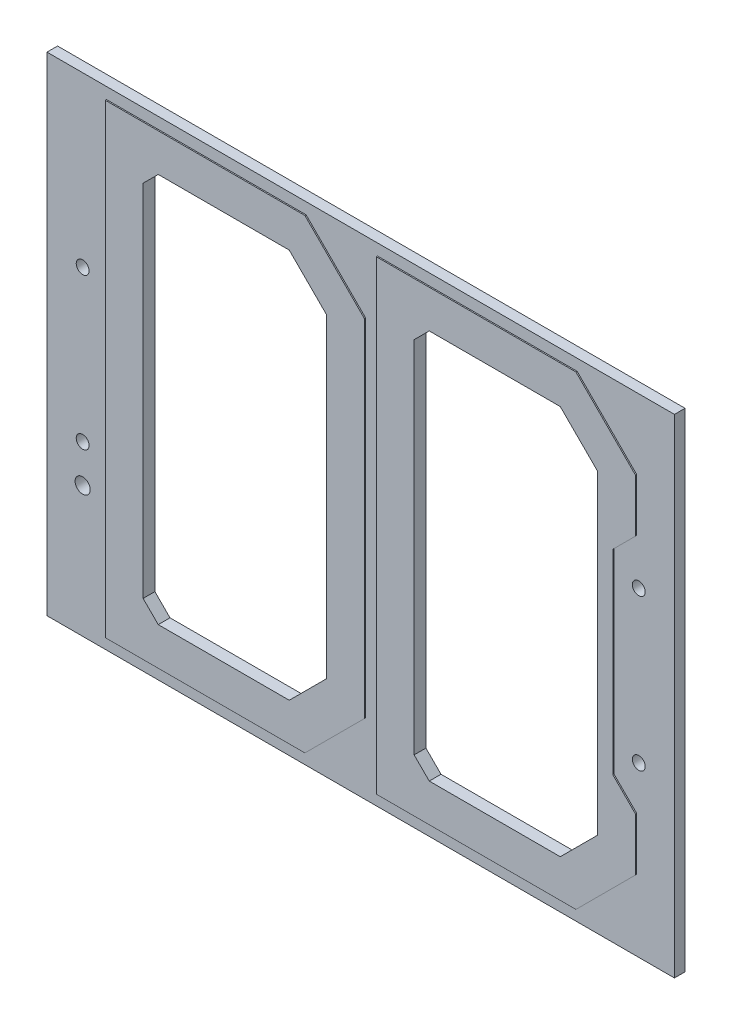
SolidWorks part; units mm, degrees
ref_plane "Front Plane" through (0, 0, 0) normal (0, 0, 1) x (1, 0, 0)
ref_plane "Top Plane" through (0, 0, 0) normal (0, 1, 0) x (1, 0, 0)
ref_plane "Right Plane" through (0, 0, 0) normal (1, 0, 0) x (0, 0, -1)
sketch "Sketch1" plane through (0, 0, 0) normal (0, 0, 1) x (1, 0, 0)
  line L0 (-46.7106, 41) -> (-46.7106, -41) construction
  line L1 (-52.705, -41) -> (52.705, -41)
  line L2 (-52.705, -41) -> (-52.705, 41)
  line L3 (-52.705, 41) -> (52.705, 41)
  line L4 (52.705, -41) -> (52.705, 41)
  line L5 (-52.705, -41) -> (52.705, 41) construction
  line L6 (-52.705, 41) -> (52.705, -41) construction
  line L7 (46.7106, 41) -> (46.7106, -41) construction
  circle A3 centre (46.7106, 12.7) radius 1.0795
  circle A4 centre (46.7106, -12.7) radius 1.0795
  circle A5 centre (-46.7106, 12.7) radius 1.0795
  circle A6 centre (-46.7106, -12.7) radius 1.0795
  circle A10 centre (-46.7106, -19.05) radius 1.27
  point P0 (0, 0)
  dimension "D15" = 2.54
  dimension "D3" = 2.159
  dimension "D1" = 82
  dimension "D2" = 105.41
  dimension "D7" = 5.9944
  dimension "D11" = 5.9944
  dimension "D4" = 28.3
  dimension "D5" = 6.35
  dimension "D9" = 28.3
extrude "Boss-Extrude1" add sketch "Sketch1" along normal blind 1.778
sketch "Sketch2" plane through (0, 0, 1.778) normal (0, 0, 1) x (1, 0, 0)
  line L0 (-9.175, 39.095) -> (0.825, 29.095)
  line L1 (-42.705, 39.095) -> (-9.175, 39.095)
  line L2 (-42.705, 39.095) -> (-42.705, -39.095)
  line L3 (-42.705, -39.095) -> (-9.175, -39.095)
  line L4 (0.825, 29.095) -> (0.825, -29.095)
  line L5 (-42.705, 39.095) -> (0.825, -39.095) construction
  line L6 (-42.705, -39.095) -> (0.825, 39.095) construction
  line L11 (46.355, 20.205) -> (42.545, 16.395)
  line L12 (42.545, 16.395) -> (42.545, -16.395)
  line L17 (42.545, -16.395) -> (46.355, -20.205)
  line L18 (-52.705, 41) -> (52.705, 41) construction
  line L23 (-52.705, -41) -> (52.705, -41) construction
  line L24 (46.355, -20.205) -> (46.355, -29.095)
  line L43 (2.825, 39.095) -> (36.355, 39.095)
  line L44 (2.825, 39.095) -> (2.825, -39.095)
  line L45 (2.825, -39.095) -> (36.355, -39.095)
  line L46 (46.355, 29.095) -> (46.355, 20.205)
  line L47 (2.825, 39.095) -> (46.355, -39.095) construction
  line L48 (2.825, -39.095) -> (46.355, 39.095) construction
  line L49 (0.825, -29.095) -> (-9.175, -39.095)
  line L62 (36.355, -39.095) -> (46.355, -29.095)
  line L63 (36.355, 39.095) -> (46.355, 29.095)
  line L64 (-52.705, -41) -> (-52.705, 41) construction
  line L65 (52.705, -41) -> (52.705, 41) construction
  point P4 (-20.94, 0)
  point P39 (24.59, 0)
  point P76 (52.705, 0)
  dimension "D25" = 10
  dimension "D26" = 6.35
  dimension "D3" = 2
  dimension "D6" = 3.81
  dimension "D7" = 45
  dimension "D8" = 45
  dimension "D9" = 8.89
  dimension "D10" = 8.89
  dimension "D11" = 1.905
  dimension "D12" = 1.905
extrude "Boss-Extrude2" add sketch "Sketch2" along normal blind 0.2
sketch "Sketch3" plane through (0, 0, 1.978) normal (0, 0, 1) x (1, 0, 0)
  line L0 (-36.355, -32.745) -> (-36.355, 32.745)
  line L1 (-36.355, 32.745) -> (-11.8053, 32.745)
  line L2 (-11.8053, 32.745) -> (-5.525, 26.4647)
  line L3 (-5.525, 26.4647) -> (-5.525, -26.4647)
  line L4 (-5.525, -26.4647) -> (-11.8053, -32.745)
  line L5 (-11.8053, -32.745) -> (-36.355, -32.745)
  line L6 (9.175, -32.745) -> (9.175, 32.745)
  line L7 (9.175, 32.745) -> (33.7247, 32.745)
  line L8 (33.7247, 32.745) -> (40.005, 26.4647)
  line L9 (40.005, 26.4647) -> (40.005, -26.4647)
  line L10 (40.005, -26.4647) -> (33.7247, -32.745)
  line L11 (33.7247, -32.745) -> (9.175, -32.745)
  line L12 (-9.175, -39.095) -> (0.825, -29.095) construction
  line L13 (0.825, 29.095) -> (-9.175, 39.095) construction
  line L14 (-42.705, 39.095) -> (-42.705, -39.095) construction
  line L15 (0.825, -29.095) -> (0.825, 29.095) construction
  line L16 (-9.175, 39.095) -> (-42.705, 39.095) construction
  line L17 (0.825, 29.095) -> (-9.175, 39.095) construction
  line L18 (-42.705, -39.095) -> (-9.175, -39.095) construction
  line L19 (2.825, 39.095) -> (2.825, -39.095) construction
  dimension "D5" = 6.35
  dimension "D1" = 6.35
  dimension "D2" = 6.35
  dimension "D3" = 6.35
  dimension "D4" = 6.35
  dimension "D6" = 6.35
extrude "Cut-Extrude1" cut sketch "Sketch3" against normal through all
chamfer "Chamfer1" distance 2.54 angle 45 4 edges at (9.175, -32.745, 0.989) (-36.355, -32.745, 0.989) (9.175, 32.745, 0.989) (-36.355, 32.745, 0.989)
equation "\"D8@Sketch1\"=\"D6@Sketch1\""
equation "\"D4@Sketch1\"=(\"D1@Sketch1\"-\"D6@Sketch1\")/2"
equation "\"D9@Sketch1\"=\"D4@Sketch1\""
equation "\"D2@Sketch3\"=\"D1@Sketch3\""
equation "\"D3@Sketch3\"=\"D1@Sketch3\""
equation "\"D4@Sketch3\"=\"D3@Sketch3\""
equation "\"D5@Sketch3\"=\"D1@Sketch3\""
equation "\"D6@Sketch3\"=\"D1@Sketch3\""
equation "\"D7@Sketch1\"=.754/2-.141"
equation "\"D10@Sketch2\"=\"D9@Sketch2\""
